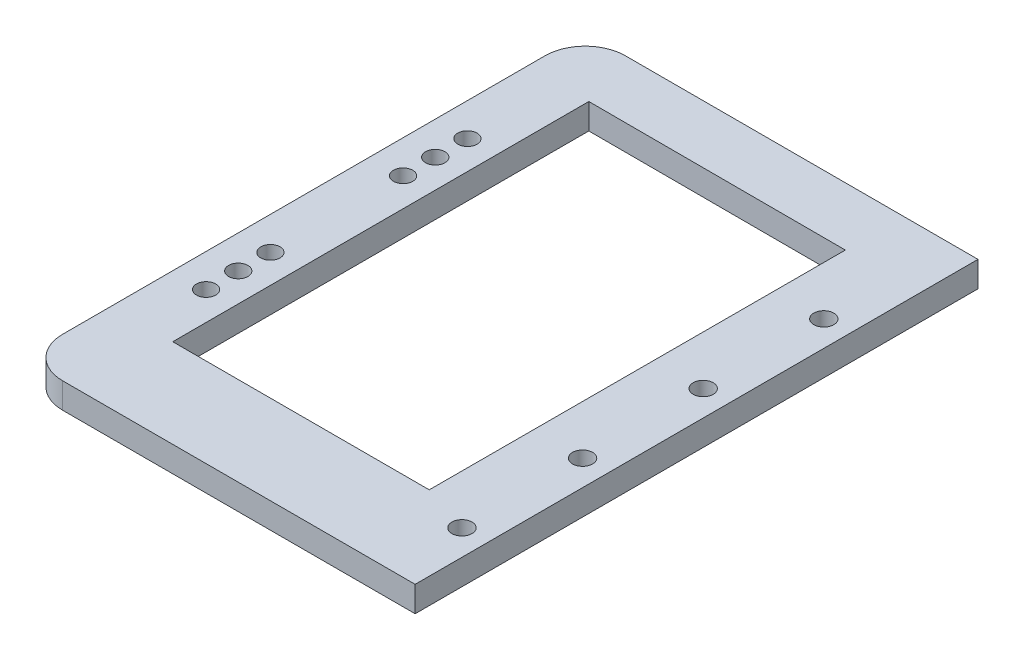
SolidWorks part; units mm, degrees
material "Acrylic (Medium-high impact)"
ref_plane "Front Plane" through (0, 0, 0) normal (0, 0, 1) x (1, 0, 0)
ref_plane "Top Plane" through (0, 0, 0) normal (0, 1, 0) x (1, 0, 0)
ref_plane "Right Plane" through (0, 0, 0) normal (1, 0, 0) x (0, 0, -1)
sketch "Sketch1" plane through (0, 0, 0) normal (0, 1, 0) x (1, 0, 0)
  line L1 (-44.8562, 77.8914) -> (52.8438, 77.8914)
  line L2 (-44.8562, 77.8914) -> (-44.8562, -62.1086)
  line L3 (-44.8562, -62.1086) -> (52.8438, -62.1086)
  line L4 (52.8438, 77.8914) -> (52.8438, -62.1086)
  dimension "D1" = 140
  dimension "D2" = 97.7
extrude "Boss-Extrude1" add sketch "Sketch1" along normal blind 6.35
fillet "Fillet1" radius 10 2 edges at (-44.8562, 3.175, 62.1086) (-44.8562, 3.175, -77.8914)
sketch "Sketch2" plane through (0, 6.35, 0) normal (0, 1, 0) x (1, 0, 0)
  line L0 (34.2438, 14.0205) -> (34.2438, 11.6417) construction
  line L1 (34.2438, 16.6958) -> (34.2438, 14.0205) construction
  line L2 (-29.5562, 11.6417) -> (-29.5562, 14.0205) construction
  line L3 (-29.5562, 14.0205) -> (-29.5562, 16.6958) construction
  line L4 (34.3438, 59.8914) -> (34.3438, 63.3914) construction
  line L5 (-29.5562, 59.8914) -> (-29.5562, 63.4914) construction
  line L6 (-29.5562, 63.4914) -> (34.2438, 63.4914) construction
  line L7 (34.2438, 59.8914) -> (34.2438, 16.6958) construction
  line L8 (-29.5562, 16.6958) -> (-29.5562, 59.8914) construction
  line L9 (34.2438, 14.0205) -> (34.2438, 11.6417)
  line L10 (34.2438, 16.6958) -> (34.2438, 14.0205)
  line L11 (-29.5562, 11.6417) -> (-29.5562, 14.0205)
  line L12 (-29.5562, 14.0205) -> (-29.5562, 16.6958)
  line L13 (34.3438, 59.8914) -> (34.3438, 63.3914)
  line L14 (-29.5562, 59.8914) -> (-29.5562, 63.4914)
  line L15 (-29.5562, 63.4914) -> (34.2438, 63.4914)
  line L16 (34.2438, 59.8914) -> (34.2438, 16.6958)
  line L17 (-29.5562, 16.6958) -> (-29.5562, 59.8914)
  line L18 (-29.5562, 11.6417) -> (-29.5562, -40)
  line L19 (-29.5562, -40) -> (34.2438, -40)
  line L20 (34.2438, -40) -> (34.2438, 11.6417)
  dimension "D1" = 40
sketch "Sketch3" plane through (0, 6.35, 0) normal (0, 1, 0) x (1, 0, 0)
  line L0 (-29.5562, 63.4914) -> (-29.5562, -40)
  line L1 (-29.5562, -40) -> (34.2438, -40)
  line L2 (34.2438, -40) -> (34.3438, 63.3914)
  line L3 (34.3438, 63.3914) -> (-29.5562, 63.4914)
extrude "Cut-Extrude1" cut sketch "Sketch3" against normal blind 6.35
sketch "Sketch4" plane through (0, 6.35, 0) normal (0, 1, 0) x (1, 0, 0)
  line L0 (-33.5562, 23.8914) -> (-33.5562, 39.8914) construction
  line L1 (-33.5562, 23.8914) -> (-33.5562, 39.8914)
  line L2 (-32.8562, -26.5086) -> (-32.8562, -21.7086) construction
  line L3 (-32.8562, -18.5086) -> (-32.8562, -13.7086) construction
  line L4 (-32.8562, -10.5086) -> (-32.8562, -5.7086) construction
  line L5 (-32.8562, 26.2914) -> (-32.8562, 21.4914) construction
  line L6 (-33.5562, 39.8914) -> (-33.5562, 43.4914) construction
  line L7 (-29.5562, 43.4914) -> (-33.5562, 43.4914) construction
  line L8 (-32.8562, -26.5086) -> (-32.8562, -21.7086)
  line L9 (-32.8562, -18.5086) -> (-32.8562, -13.7086)
  line L10 (-32.8562, -10.5086) -> (-32.8562, -5.7086)
  line L11 (-32.8562, 26.2914) -> (-32.8562, 21.4914)
  line L12 (-33.5562, 39.8914) -> (-33.5562, 43.4914)
  line L13 (-29.5562, 43.4914) -> (-33.5562, 43.4914)
  line L14 (-33.6562, -8.1086) -> (-33.6562, -24.1086) construction
  line L15 (-33.6562, -11.3086) -> (-33.6562, -4.9086) construction
  line L16 (-33.6562, -8.1086) -> (-33.6562, -24.1086)
  line L17 (-33.6562, -11.3086) -> (-33.6562, -4.9086)
  line L18 (-29.5562, -27.7086) -> (-33.5562, -27.7086) construction
  line L19 (-33.5562, -24.1086) -> (-33.5562, -27.7086) construction
  line L20 (-29.5562, -27.7086) -> (-33.5562, -27.7086)
  line L21 (-33.5562, -24.1086) -> (-33.5562, -27.7086)
sketch "Sketch5" plane through (0, 6.35, 0) normal (0, 1, 0) x (1, 0, 0)
  line L0 (-29.5562, 43.4914) -> (-33.5562, 43.4914) construction
  line L1 (-33.5562, 23.8914) -> (-33.5562, 39.8914) construction
  line L2 (-29.5562, -27.7086) -> (-33.5562, -27.7086) construction
  line B0 (-39.7562, 24.3914) -> (-39.7562, 40.3914)
  line B1 (-33.5562, 24.3914) -> (-33.5562, 40.3914)
  circle B2 centre (-36.6562, 40.3914) radius 2.4
  circle B3 centre (-36.6562, 32.3914) radius 2.4
  circle B4 centre (-36.6562, 24.3914) radius 2.4
  arc B5 (-39.7562, 24.3914) -> (-33.5562, 24.3914) centre (-36.6562, 24.3914) ccw
  arc B6 (-33.5562, 40.3914) -> (-39.7562, 40.3914) centre (-36.6562, 40.3914) ccw
  line B7 (-39.7562, -24.6086) -> (-39.7562, -8.6086)
  line B8 (-33.5562, -24.6086) -> (-33.5562, -8.6086)
  circle B9 centre (-36.6562, -8.6086) radius 2.4
  circle B10 centre (-36.6562, -16.6086) radius 2.4
  circle B11 centre (-36.6562, -24.6086) radius 2.4
  arc B12 (-39.7562, -24.6086) -> (-33.5562, -24.6086) centre (-36.6562, -24.6086) ccw
  arc B13 (-33.5562, -8.6086) -> (-39.7562, -8.6086) centre (-36.6562, -8.6086) ccw
sketch_block_instance "Block-3HolePiece-1"
sketch_block "Block-3HolePiece"
sketch_block_instance "Block-3HolePiece-3"
extrude "Cut-Extrude2" cut sketch "Sketch5" against normal blind 6.35 contours B2 | B4 | B9 | B11 | B10 | B3
hole_wizard "Ø5.0mm Dowel Hole1" positions "Sketch11" profile "Sketch12" hole size "Ø5.0" standard "ANSI Metric"
sketch "Sketch11" plane through (0, 6.35, 0) normal (0, 1, 0) x (1, 0, 0)
  line L0 (52.8438, -62.1086) -> (52.8438, 77.8914) construction
  point P0 (46.4938, 45.8881)
  point P12 (46.4938, 15.8881)
  point P13 (46.4938, -14.1119)
  point P14 (46.4938, -44.1119)
  dimension "D1" = 6.35
  dimension "D2" = 4
sketch "Sketch12" plane through (46.4938, 6.35, -45.8881) normal (1, 0, 0) x (0, 0, 1)
  line L0 (0, 0) -> (0, 11.5022)
  line L1 (0, 11.5022) -> (2.5, 10)
  line L2 (2.5, 10) -> (2.5, 0)
  line L5 (2.5, 0) -> (0, 0)
  line L10 (0, 11.5022) -> (-2.5, 10) construction
  line L11 (0, -6.35) -> (0, 107.95) construction
  dimension "Hole Dia." = 5
  dimension "Hole Depth" = 10
  dimension "Drill Angle" = 118
